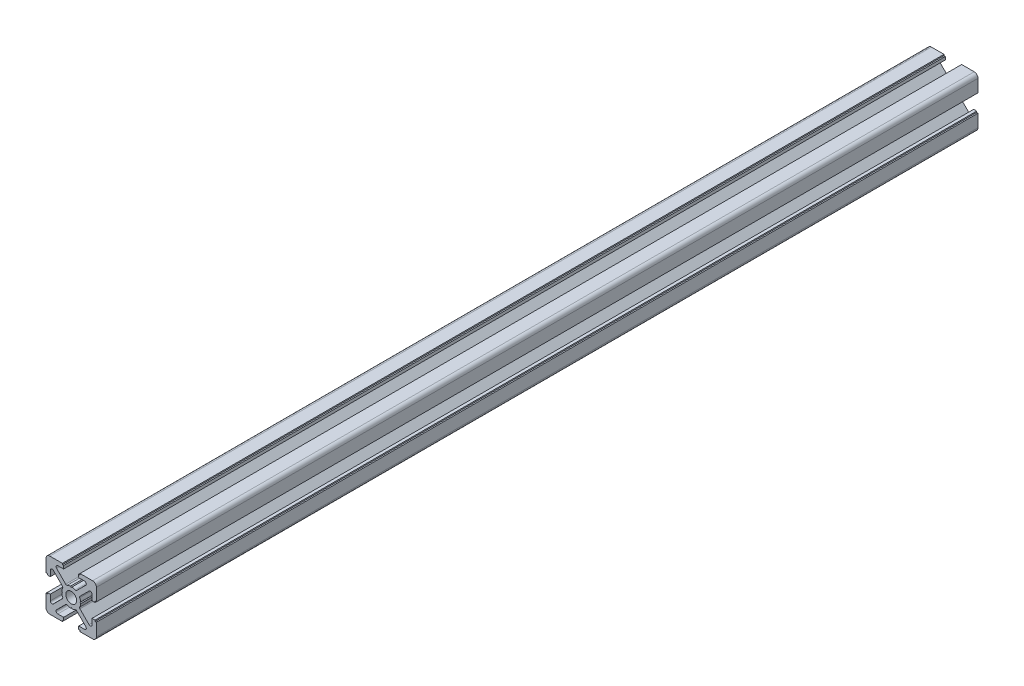
SolidWorks part; units mm, degrees
ref_plane "Alzado" through (0, 0, 0) normal (0, 0, 1) x (1, 0, 0)
ref_plane "Planta" through (0, 0, 0) normal (0, 1, 0) x (1, 0, 0)
ref_plane "Vista lateral" through (0, 0, 0) normal (1, 0, 0) x (0, 0, -1)
sketch "Model" plane through (0, 0, 0) normal (0, 0, 1) x (1, 0, 0)
  line L0 (-3.5, -9.5) -> (-3.5, -10)
  line L1 (-3.5, -10) -> (-8.5, -10)
  line L2 (-10, -8.5) -> (-10, -3.5)
  line L3 (-10, -3.5) -> (-9.5, -3.5)
  line L4 (-9.5, -3.5) -> (-9.5, -3)
  line L5 (-9.5, -3) -> (-8.3, -3)
  line L6 (-8.3, -3) -> (-8.3, -5.2994)
  line L7 (-7.105, -5.7944) -> (-3.4861, -2.1755)
  line L8 (-3.738, -0.3) -> (-3.45, 0)
  line L9 (-3.45, 0) -> (-3.738, 0.3)
  line L10 (-3.4861, 2.1755) -> (-7.105, 5.7944)
  line L11 (-8.3, 5.2994) -> (-8.3, 3)
  line L12 (-8.3, 3) -> (-9.5, 3)
  line L13 (-9.5, 3) -> (-9.5, 3.5)
  line L14 (-9.5, 3.5) -> (-10, 3.5)
  line L15 (-10, 3.5) -> (-10, 8.5)
  line L16 (-8.5, 10) -> (-3.5, 10)
  line L17 (-3.5, 10) -> (-3.5, 9.5)
  line L18 (-3.5, 9.5) -> (-3, 9.5)
  line L19 (-3, 9.5) -> (-3, 8.3)
  line L20 (-3, 8.3) -> (-5.2994, 8.3)
  line L21 (-5.7944, 7.105) -> (-2.1755, 3.4861)
  line L22 (-0.3, 3.738) -> (0, 3.45)
  line L23 (0, 3.45) -> (0.3, 3.738)
  line L24 (2.1755, 3.4861) -> (5.7944, 7.105)
  line L25 (5.2994, 8.3) -> (3, 8.3)
  line L26 (3, 8.3) -> (3, 9.5)
  line L27 (3, 9.5) -> (3.5, 9.5)
  line L28 (3.5, 9.5) -> (3.5, 10)
  line L29 (3.5, 10) -> (8.5, 10)
  line L30 (10, 8.5) -> (10, 3.5)
  line L31 (10, 3.5) -> (9.5, 3.5)
  line L32 (9.5, 3.5) -> (9.5, 3)
  line L33 (9.5, 3) -> (8.3, 3)
  line L34 (8.3, 3) -> (8.3, 5.2994)
  line L35 (7.105, 5.7944) -> (3.4861, 2.1755)
  line L36 (3.738, 0.3) -> (3.45, 0)
  line L37 (3.45, 0) -> (3.738, -0.3)
  line L38 (3.4861, -2.1755) -> (7.105, -5.7944)
  line L39 (8.3, -5.2994) -> (8.3, -3)
  line L40 (8.3, -3) -> (9.5, -3)
  line L41 (9.5, -3) -> (9.5, -3.5)
  line L42 (9.5, -3.5) -> (10, -3.5)
  line L43 (10, -3.5) -> (10, -8.5)
  line L44 (8.5, -10) -> (3.5, -10)
  line L45 (3.5, -10) -> (3.5, -9.5)
  line L46 (3.5, -9.5) -> (3, -9.5)
  line L47 (3, -9.5) -> (3, -8.3)
  line L48 (3, -8.3) -> (5.2994, -8.3)
  line L49 (5.7944, -7.105) -> (2.1755, -3.4861)
  line L50 (0.3, -3.738) -> (0, -3.45)
  line L51 (0, -3.45) -> (-0.3, -3.738)
  line L52 (-2.1755, -3.4861) -> (-5.7944, -7.105)
  line L53 (-5.2994, -8.3) -> (-3, -8.3)
  line L54 (-3, -8.3) -> (-3, -9.5)
  line L55 (-3, -9.5) -> (-3.5, -9.5)
  arc A0 (-5.7944, -7.105) -> (-5.9994, -7.6) centre (-5.2994, -7.6) ccw
  arc A1 (5.9994, -7.6) -> (5.7944, -7.105) centre (5.2994, -7.6) ccw
  arc A2 (3.388, -1.6076) -> (3.3397, -1.8219) centre (3.8397, -1.8219) ccw
  arc A3 (3.4861, 2.1755) -> (3.3397, 1.8219) centre (3.8397, 1.8219) ccw
  arc A4 (5.9994, 7.6) -> (5.2994, 8.3) centre (5.2994, 7.6) ccw
  arc A5 (-5.2994, 8.3) -> (-5.9994, 7.6) centre (-5.2994, 7.6) ccw
  arc A6 (-3.3397, 1.8219) -> (-3.4861, 2.1755) centre (-3.8397, 1.8219) ccw
  arc A7 (-3.3397, -1.8219) -> (-3.388, -1.6076) centre (-3.8397, -1.8219) ccw
  arc A8 (-2.15, 0) -> (2.15, 0) centre (0, 0) ccw
  arc A9 (2.15, 0) -> (-2.15, 0) centre (0, 0) ccw
  arc A10 (-10, -8.5) -> (-8.5, -10) centre (-8.5, -8.5) ccw
  arc A11 (-8.3, -5.2994) -> (-7.105, -5.7944) centre (-7.6, -5.2994) ccw
  arc A12 (-3.4861, -2.1755) -> (-3.3397, -1.8219) centre (-3.8397, -1.8219) ccw
  arc A13 (-3.738, -0.3) -> (-3.388, -1.6076) centre (0, 0) ccw
  arc A14 (-3.388, 1.6076) -> (-3.738, 0.3) centre (0, 0) ccw
  arc A15 (-3.388, 1.6076) -> (-3.3397, 1.8219) centre (-3.8397, 1.8219) ccw
  arc A16 (-7.105, 5.7944) -> (-8.3, 5.2994) centre (-7.6, 5.2994) ccw
  arc A17 (-8.5, 10) -> (-10, 8.5) centre (-8.5, 8.5) ccw
  arc A18 (-5.9994, 7.6) -> (-5.7944, 7.105) centre (-5.2994, 7.6) ccw
  arc A19 (-2.1755, 3.4861) -> (-1.6076, 3.388) centre (-1.8219, 3.8397) ccw
  arc A20 (-0.3, 3.738) -> (-1.6076, 3.388) centre (0, 0) ccw
  arc A21 (1.6076, 3.388) -> (0.3, 3.738) centre (0, 0) ccw
  arc A22 (1.6076, 3.388) -> (2.1755, 3.4861) centre (1.8219, 3.8397) ccw
  arc A23 (5.7944, 7.105) -> (5.9994, 7.6) centre (5.2994, 7.6) ccw
  arc A24 (10, 8.5) -> (8.5, 10) centre (8.5, 8.5) ccw
  arc A25 (8.3, 5.2994) -> (7.105, 5.7944) centre (7.6, 5.2994) ccw
  arc A26 (3.3397, 1.8219) -> (3.388, 1.6076) centre (3.8397, 1.8219) ccw
  arc A27 (3.738, 0.3) -> (3.388, 1.6076) centre (0, 0) ccw
  arc A28 (3.388, -1.6076) -> (3.738, -0.3) centre (0, 0) ccw
  arc A29 (3.3397, -1.8219) -> (3.4861, -2.1755) centre (3.8397, -1.8219) ccw
  arc A30 (7.105, -5.7944) -> (8.3, -5.2994) centre (7.6, -5.2994) ccw
  arc A31 (8.5, -10) -> (10, -8.5) centre (8.5, -8.5) ccw
  arc A32 (5.2994, -8.3) -> (5.9994, -7.6) centre (5.2994, -7.6) ccw
  arc A33 (2.1755, -3.4861) -> (1.6076, -3.388) centre (1.8219, -3.8397) ccw
  arc A34 (0.3, -3.738) -> (1.6076, -3.388) centre (0, 0) ccw
  arc A35 (-1.6076, -3.388) -> (-0.3, -3.738) centre (0, 0) ccw
  arc A36 (-1.6076, -3.388) -> (-2.1755, -3.4861) centre (-1.8219, -3.8397) ccw
  arc A37 (-5.9994, -7.6) -> (-5.2994, -8.3) centre (-5.2994, -7.6) ccw
  point P115 (0, 0)
  dimension "D1" = 10
  dimension "D2" = 10
extrude "Saliente-Extruir1" add sketch "Model" along normal blind 350
